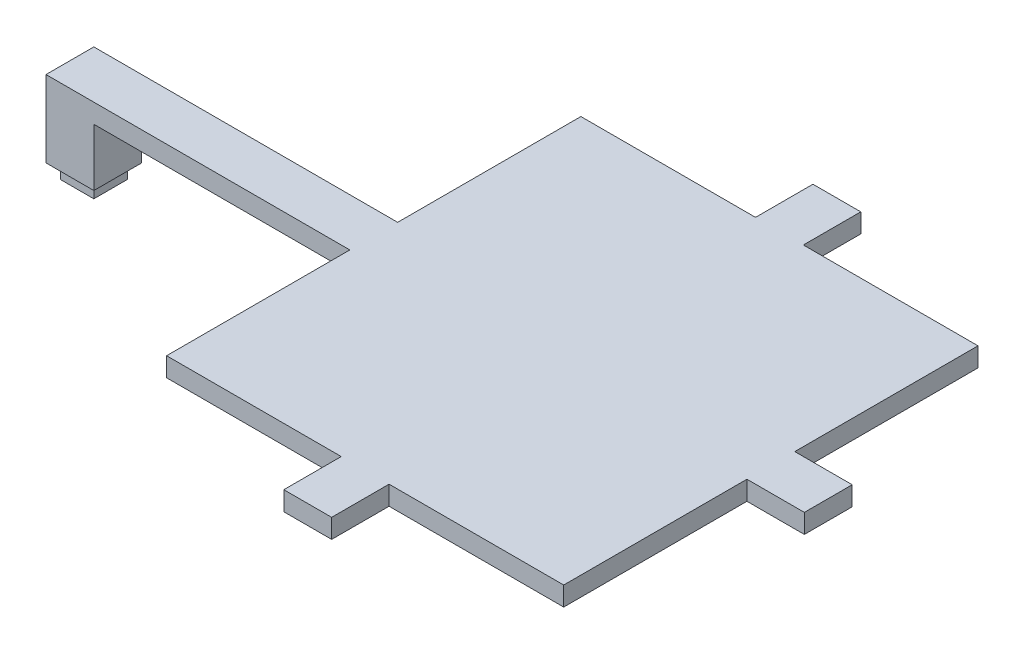
SolidWorks part; units mm, degrees
ref_plane "Front Plane" through (0, 0, 0) normal (0, 0, 1) x (1, 0, 0)
ref_plane "Top Plane" through (0, 0, 0) normal (0, 1, 0) x (1, 0, 0)
ref_plane "Right Plane" through (0, 0, 0) normal (1, 0, 0) x (0, 0, -1)
sketch "Sketch1" plane through (0, 0, 0) normal (0, 1, 0) x (1, 0, 0)
  line L5 (-3.5, -3.5) -> (3.5, -3.5)
  line L6 (-3.5, -3.5) -> (-3.5, 3.5)
  line L7 (-3.5, 3.5) -> (3.5, 3.5)
  line L8 (3.5, -3.5) -> (3.5, 3.5)
  line L9 (-3.5, -3.5) -> (3.5, 3.5) construction
  line L10 (-3.5, 3.5) -> (3.5, -3.5) construction
  point P0 (0, 0)
extrude "Boss-Extrude1" add sketch "Sketch1" along normal blind 3
sketch "Sketch3" plane through (0, 3, 0) normal (0, 1, 0) x (1, 0, 0)
  line L1 (-5, -5) -> (5, -5)
  line L2 (-5, -5) -> (-5, 5)
  line L3 (-5, 5) -> (5, 5)
  line L4 (5, -5) -> (5, 5)
  line L5 (-5, -5) -> (5, 5) construction
  line L6 (-5, 5) -> (5, -5) construction
  point P0 (0, 0)
extrude "Boss-Extrude2" add sketch "Sketch3" along normal blind 12
sketch "Sketch4" plane through (0, 15, 0) normal (0, 1, 0) x (1, 0, 0)
  line L0 (0, 0) -> (100, 0) construction
  line L5 (105, 43.2945) -> (105, 55.2945)
  line L10 (58.5, 43.2945) -> (58.5, -43.2945)
  line L11 (141.5, 43.2945) -> (58.5, -43.2945) construction
  line L12 (141.5, -43.2945) -> (58.5, 43.2945) construction
  line L13 (95, -43.2945) -> (95, -55.2945)
  line L14 (95, -55.2945) -> (105, -55.2945)
  line L15 (105, -43.2945) -> (105, -55.2945)
  line L16 (141.5, 5) -> (141.5, 43.2945)
  line L17 (141.5, 43.2945) -> (105, 43.2945)
  line L18 (105, 55.2945) -> (95, 55.2945)
  line L19 (95, 55.2945) -> (95, 43.2945)
  line L20 (95, 43.2945) -> (58.5, 43.2945)
  line L21 (141.5, 5) -> (153.5, 5)
  line L23 (141.5, -5) -> (153.5, -5)
  line L24 (153.5, 5) -> (153.5, -5)
  line L25 (141.5, -5) -> (141.5, -43.2945)
  line L26 (141.5, -43.2945) -> (105, -43.2945)
  line L27 (95, -43.2945) -> (58.5, -43.2945)
  point P0 (0, 0)
  point P8 (5.8574, -43.2945)
  point P17 (47.3574, 0)
extrude "Boss-Extrude4" add sketch "Sketch4" along normal blind 4
sketch "Sketch5" plane through (5, 0, 0) normal (1, 0, 0) x (0, 0, -1)
  line L0 (5, 15) -> (5, 3) construction
  line L1 (-5, 15) -> (5, 15)
  line L2 (-5, 15) -> (-5, 8)
  line L3 (-5, 8) -> (5, 8)
  line L4 (5, 15) -> (5, 8)
sketch "Sketch7" plane through (0, 15, 0) normal (0, 1, 0) x (1, 0, 0)
  line L1 (-5, 5) -> (5, 5)
  line L2 (-5, 5) -> (-5, -5)
  line L3 (-5, -5) -> (5, -5)
  line L4 (5, 5) -> (5, -5)
extrude "Boss-Extrude6" add sketch "Sketch7" along normal blind 4
sketch "Sketch8" plane through (5, 0, 0) normal (1, 0, 0) x (0, 0, -1)
  line L1 (5, 19) -> (-5, 19)
  line L2 (5, 19) -> (5, 15)
  line L3 (5, 15) -> (-5, 15)
  line L4 (-5, 19) -> (-5, 15)
extrude "Boss-Extrude7" add sketch "Sketch8" along normal up to vertex (53.5 mm away)
